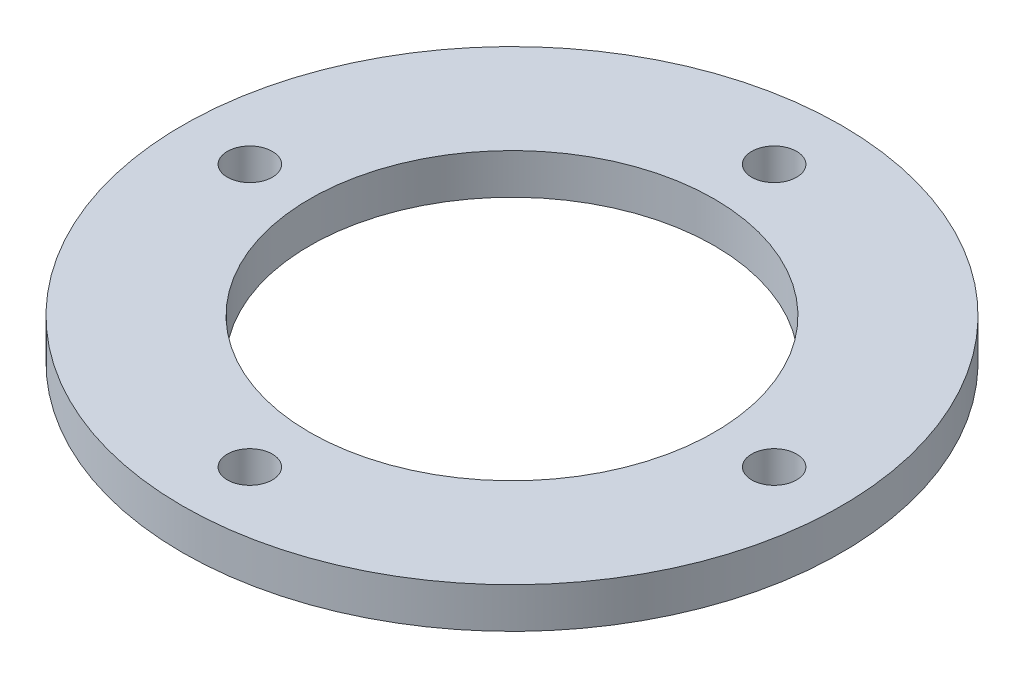
SolidWorks part; units mm, degrees
material "6061 合金"
ref_plane "前视基准面" through (0, 0, 0) normal (0, 0, 1) x (1, 0, 0)
ref_plane "上视基准面" through (0, 0, 0) normal (0, 1, 0) x (1, 0, 0)
ref_plane "右视基准面" through (0, 0, 0) normal (1, 0, 0) x (0, 0, -1)
sketch "草图1" plane through (0, 0, 0) normal (0, 1, 0) x (1, 0, 0)
  circle A0 centre (0, 0) radius 17.5 construction
  circle A1 centre (17.5, 0) radius 1.5
  circle A2 centre (0, -17.5) radius 1.5
  circle A3 centre (-17.5, 0) radius 1.5
  circle A18 centre (0, 17.5) radius 1.5
  circle A20 centre (0, 0) radius 13.5
  circle A41 centre (0, 0) radius 22
  dimension "D3" = 35
  dimension "D4" = 3
  dimension "D6" = 27
  dimension "D7" = 22
  dimension "D5" = 4
extrude "凸台-拉伸1" add sketch "草图1" along normal blind 2.7
